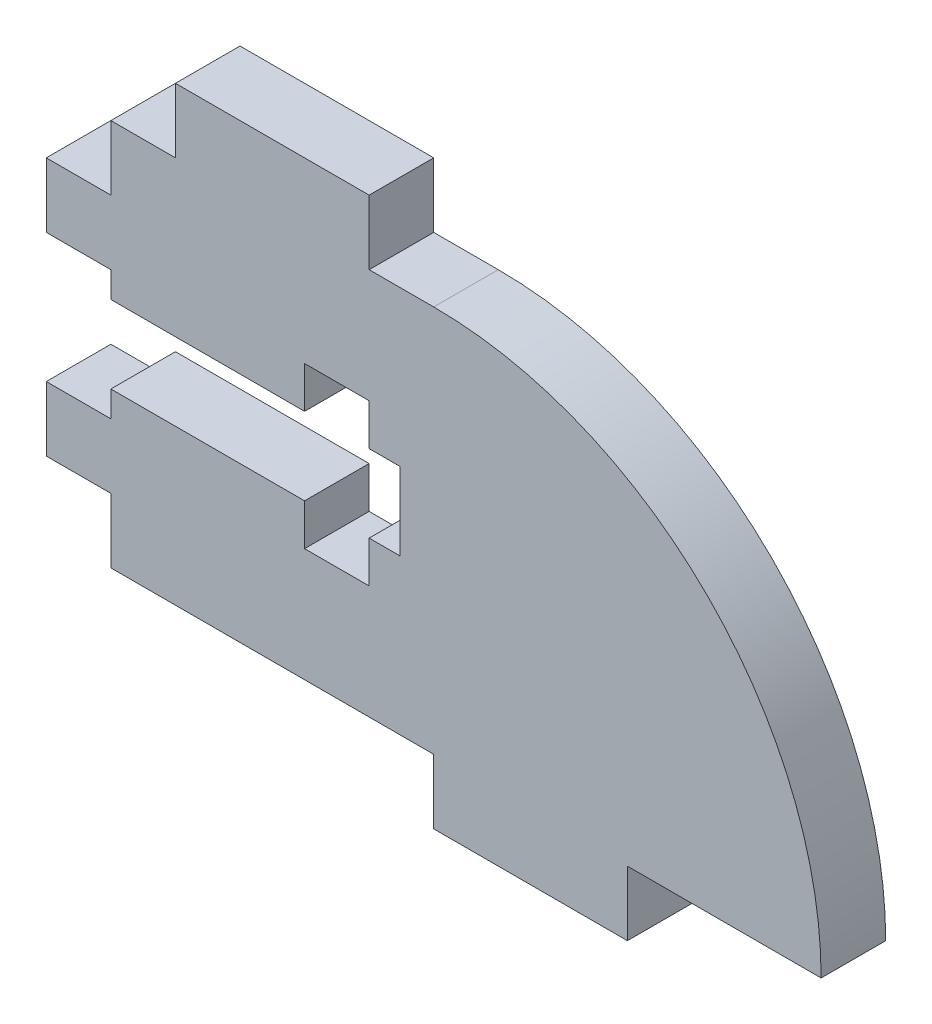
SolidWorks part; units mm, degrees
ref_plane "Front Plane" through (0, 0, 0) normal (0, 0, 1) x (1, 0, 0)
ref_plane "Top Plane" through (0, 0, 0) normal (0, 1, 0) x (1, 0, 0)
ref_plane "Right Plane" through (0, 0, 0) normal (1, 0, 0) x (0, 0, -1)
sketch "Sketch1" plane through (0, 0, 0) normal (0, 0, 1) x (1, 0, 0)
  line L0 (0, 0) -> (0, 3.175)
  line L1 (0, 0) -> (15.875, 0)
  line L2 (0, 19.05) -> (3.175, 19.05)
  line L3 (3.175, 19.05) -> (3.175, 22.225)
  line L4 (3.175, 22.225) -> (12.7, 22.225)
  line L5 (12.7, 22.225) -> (12.7, 19.05)
  line L6 (12.7, 19.05) -> (15.875, 19.05)
  line L7 (15.875, 0) -> (15.875, -3.175)
  line L8 (15.875, -3.175) -> (25.4, -3.175)
  line L9 (25.4, -3.175) -> (25.4, 0)
  line L10 (25.4, 0) -> (34.925, 0)
  line L11 (14.224, 9.525) -> (37.0174, 9.525) construction
  line L12 (0, 11.43) -> (9.525, 11.43)
  line L13 (9.525, 11.43) -> (9.525, 13.4675)
  line L14 (9.525, 13.4675) -> (12.7, 13.4675)
  line L15 (12.7, 13.4675) -> (12.7, 11.43)
  line L16 (12.7, 11.43) -> (14.224, 11.43)
  line L17 (14.224, 11.43) -> (14.224, 7.62)
  line L18 (0, 12.7) -> (-3.175, 12.7)
  line L19 (-3.175, 12.7) -> (-3.175, 15.875)
  line L20 (-3.175, 15.875) -> (0, 15.875)
  line L21 (12.7, 5.5825) -> (12.7, 7.62)
  line L22 (12.7, 7.62) -> (14.224, 7.62)
  line L23 (9.525, 5.5825) -> (12.7, 5.5825)
  line L24 (9.525, 7.62) -> (9.525, 5.5825)
  line L25 (0, 7.62) -> (9.525, 7.62)
  line L26 (0, 6.35) -> (-3.175, 6.35)
  line L27 (-3.175, 6.35) -> (-3.175, 3.175)
  line L28 (-3.175, 3.175) -> (0, 3.175)
  line L29 (0, 11.43) -> (0, 12.7)
  line L30 (0, 15.875) -> (0, 19.05)
  line L31 (0, 6.35) -> (0, 7.62)
  arc A0 (15.875, 19.05) -> (34.925, 0) centre (15.875, 0) cw
  point P28 (14.224, 9.525)
  dimension "D1" = 19.05
  dimension "D2" = 34.925
  dimension "D3" = 15.875
  dimension "D4" = 3.175
  dimension "D5" = 9.525
  dimension "D6" = 3.175
  dimension "D7" = 3.175
  dimension "D8" = 9.525
  dimension "D9" = 3.175
  dimension "D10" = 1.905
  dimension "D11" = 12.7
  dimension "D12" = 14.224
  dimension "D13" = 3.175
  dimension "D14" = 3.175
  dimension "D15" = 3.175
  dimension "D16" = 15.875
extrude "Boss-Extrude1" add sketch "Sketch1" along normal blind 3.175
equation "\"THICK\"= 1 / 8in"
